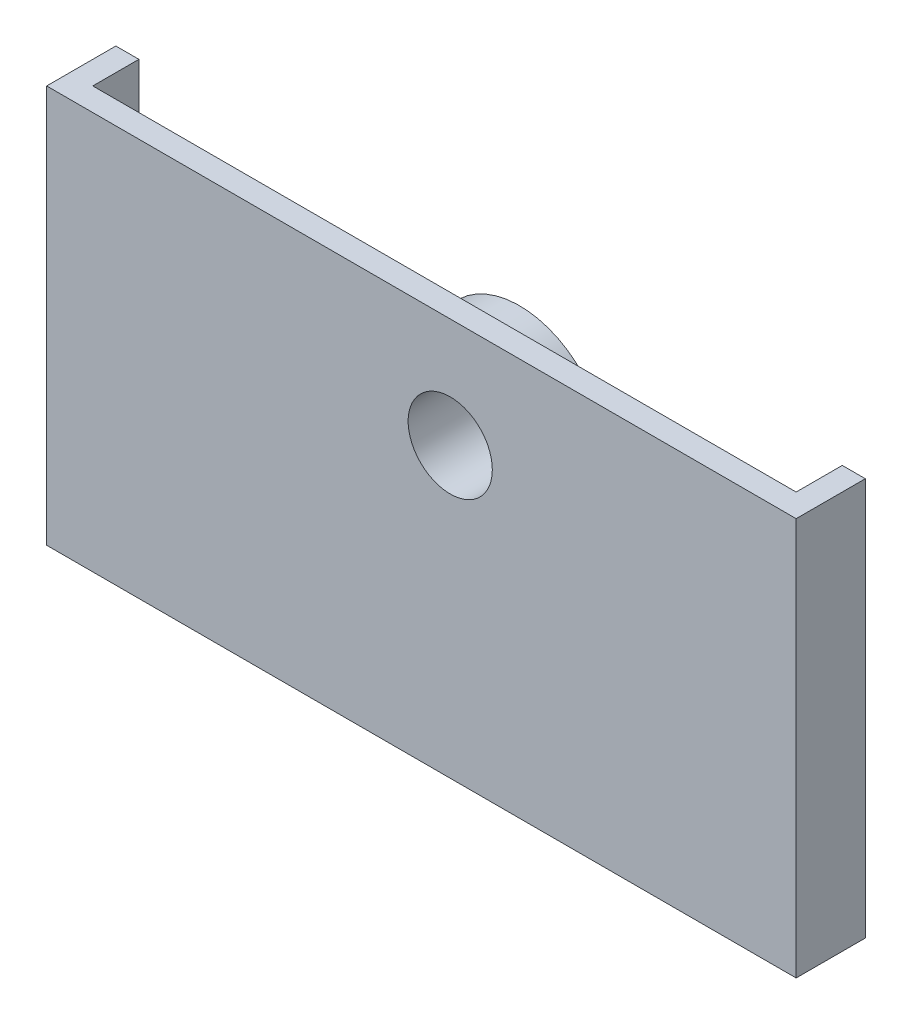
SolidWorks part; units mm, degrees
ref_plane "前视基准面" through (0, 0, 0) normal (0, 0, 1) x (1, 0, 0)
ref_plane "上视基准面" through (0, 0, 0) normal (0, 1, 0) x (1, 0, 0)
ref_plane "右视基准面" through (0, 0, 0) normal (1, 0, 0) x (0, 0, -1)
other "Configuration Table"
sketch "草图2" plane through (0, 0, 0) normal (0, 0, 1) x (1, 0, 0)
  circle A0 centre (0, 0) radius 3.65
  circle A1 centre (0, 0) radius 7.5
  dimension "D1" = 7.3
  dimension "D2" = 15
extrude "凸台-拉伸1" add sketch "草图2" along normal blind 4
sketch "草图3" plane through (0, 0, 4) normal (0, 0, 1) x (1, 0, 0)
  line L0 (30, 9.5) -> (30, -25)
  line L1 (30, -25) -> (-35, -25)
  line L2 (-35, -25) -> (-35, 9.5)
  line L3 (-35, 9.5) -> (30, 9.5)
  circle A0 centre (0, 0) radius 3.65 construction
  circle A1 centre (0, 0) radius 3.65
  circle A2 centre (0, 0) radius 7.5 construction
  dimension "D2" = 35
  dimension "D3" = 25
  dimension "D4" = 9.5
  dimension "D1" = 30
extrude "凸台-拉伸2" add sketch "草图3" along normal blind 2
sketch "草图4" plane through (0, 0, 4) normal (0, 0, -1) x (-1, 0, 0)
  line L1 (-28, 7.5) -> (-28, -23)
  line L2 (-28, -23) -> (33, -23)
  line L3 (33, -23) -> (33, 7.5)
  line L4 (35, 9.5) -> (-30, 9.5)
  line L5 (-30, 9.5) -> (-30, -25)
  line L6 (-30, -25) -> (35, -25)
  line L7 (35, -25) -> (35, 9.5)
  line L8 (35, 9.5) -> (33, 9.5)
  line L9 (-30, 9.5) -> (-30, -25)
  line L10 (-30, -25) -> (35, -25)
  line L11 (35, -25) -> (35, 9.5)
  line L12 (-28, 7.5) -> (-28, 9.5)
  line L13 (33, 7.5) -> (33, 9.5)
  line L14 (-28, 9.5) -> (-30, 9.5)
  line L15 (35, 9.5) -> (-30, 9.5) construction
  line L16 (33, 7.5) -> (-28, 7.5) construction
  dimension "D1" = 0
  dimension "D2" = 2
extrude "凸台-拉伸3" add sketch "草图4" along normal up to surface (4 mm away) up to face at (7.5, 0, 0)
sketch "草图5" plane through (0, 0, 0) normal (0, 0, -1) x (-1, 0, 0)
  line L0 (-28, -23) -> (33, -23) construction
  line L1 (-5, -23) -> (5, -23)
  line L2 (-5, -23) -> (-5, -25)
  line L3 (-5, -25) -> (5, -25)
  line L4 (5, -23) -> (5, -25)
  line L5 (35, -25) -> (-30, -25) construction
  line L6 (0, -23) -> (0, 0) construction
  dimension "D1" = 10
extrude "切除-拉伸1" cut sketch "草图5" against normal blind 3.7
fillet "圆角1" radius 1.5 2 edges at (-5, -24, 3.7) (5, -24, 3.7)
sketch "草图6" plane through (0, 0, 0) normal (0, 0, -1) x (-1, 0, 0)
  line L0 (33, -23) -> (33, 9.5) construction
  line L1 (33, 3) -> (35, 3)
  line L2 (33, 3) -> (33, -7)
  line L3 (33, -7) -> (35, -7)
  line L4 (35, 3) -> (35, -7)
  line L5 (35, 9.5) -> (35, -25) construction
  circle A0 centre (0, 0) radius 3.65 construction
  circle A1 centre (0, 0) radius 7.5 construction
  dimension "D1" = 3
  dimension "D2" = 7
extrude "切除-拉伸2" cut sketch "草图6" against normal blind 5
sketch "草图7" plane through (-33, 0, 0) normal (-1, 0, 0) x (0, 0, 1)
  line L4 (4, 3) -> (4, -7)
  line L5 (4, -7) -> (5, -7)
  line L6 (5, -7) -> (5, 3)
  line L7 (5, 3) -> (4, 3)
  line L8 (4, 3) -> (4, -7)
  line L9 (4, -7) -> (5, -7)
  line L10 (5, -7) -> (5, 3)
  line L11 (5, 3) -> (4, 3)
  dimension "D1" = 0
extrude "切除-拉伸3" cut sketch "草图7" against normal offset from surface (5.5 mm away) 7.5 up to face at (-35, -4.875, 2.75)
